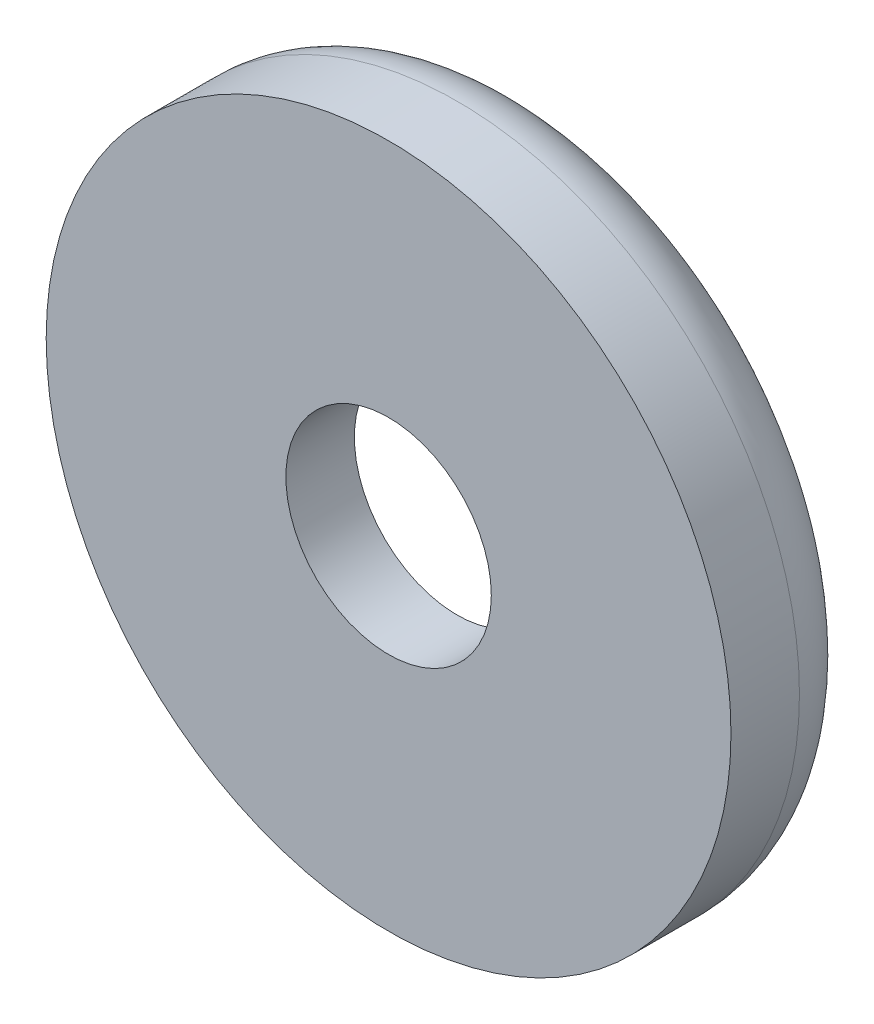
SolidWorks part; units mm, degrees
ref_plane "Front" through (0, 0, 0) normal (0, 0, 1) x (1, 0, 0)
ref_plane "Top" through (0, 0, 0) normal (0, 1, 0) x (1, 0, 0)
ref_plane "Right" through (0, 0, 0) normal (1, 0, 0) x (0, 0, -1)
sketch "Esquisse1" plane through (0, 0, 0) normal (0, 0, 1) x (1, 0, 0)
  circle A0 centre (0, 0) radius 5
  dimension "D1" = 10
extrude "Boss.-Extru.1" add sketch "Esquisse1" along normal blind 2
sketch "Esquisse2" plane through (0, 0, 0) normal (0, 0, 1) x (1, 0, 0)
  circle A0 centre (0, 0) radius 1.5
  dimension "D1" = 3
extrude "Enlèv. mat.-Extru.2" cut sketch "Esquisse2" along normal blind 13
sketch "Esquisse3" plane through (0, 0, 0) normal (0, 0, 1) x (1, 0, 0)
  circle A0 centre (0, 0) radius 3.5
extrude "Enlèv. mat.-Extru.4" cut sketch "Esquisse3" along normal blind 1
fillet "Congé1" radius 1 1 edges at (5, 0, 0)
